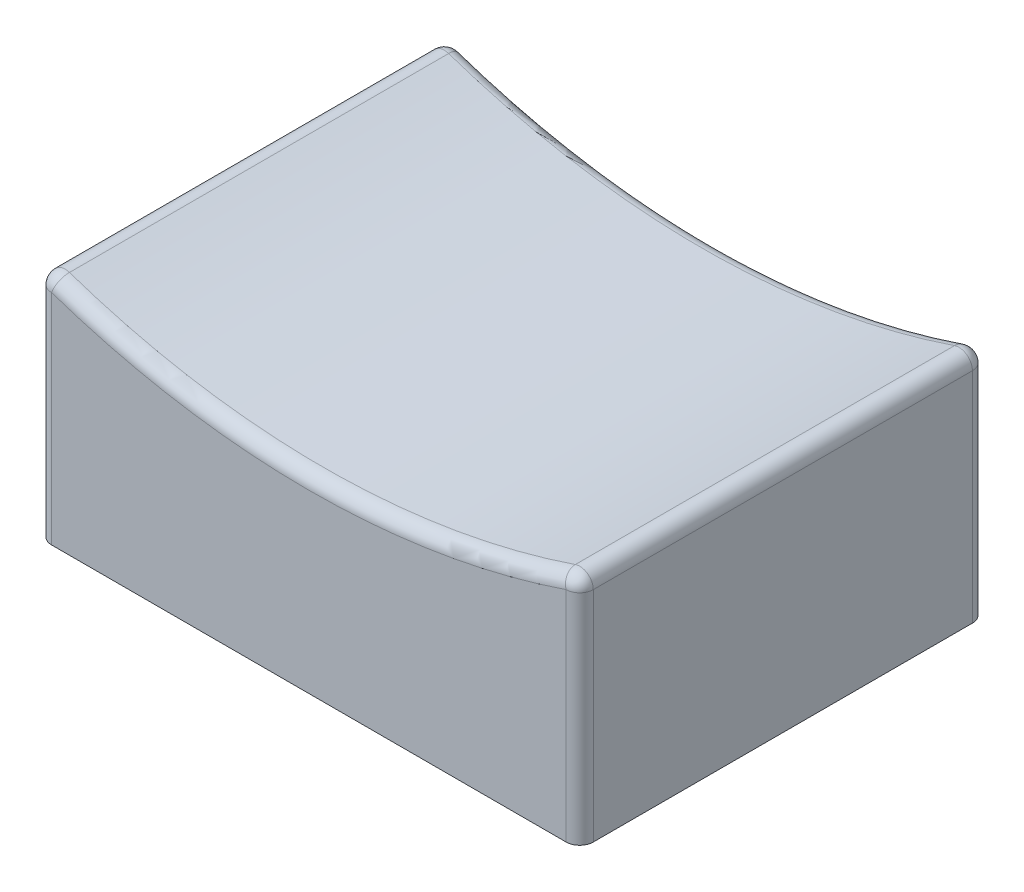
SolidWorks part; units mm, degrees
material "PBT General Purpose"
ref_plane "Front Plane" through (0, 0, 0) normal (0, 0, 1) x (1, 0, 0)
ref_plane "Top Plane" through (0, 0, 0) normal (0, 1, 0) x (1, 0, 0)
ref_plane "Right Plane" through (0, 0, 0) normal (1, 0, 0) x (0, 0, -1)
sketch "Sketch1" plane through (0, 0, 0) normal (0, 0, 1) x (1, 0, 0)
  line L0 (10, 0) -> (10, 36) construction
  line L1 (0, 0) -> (20, 0)
  line L2 (0, 0) -> (0, 8.7787)
  line L4 (20, 0) -> (20, 8.7787)
  arc A0 (0, 8.7787) -> (20, 8.7787) centre (10, 36) ccw
  point P8 (10, 7)
  dimension "D1" = 58
  dimension "D2" = 7
  dimension "D3" = 20
extrude "Boss-Extrude1" add sketch "Sketch1" along normal blind 15
fillet "Fillet1" radius 0.5 8 edges at (20, 8.7787, 7.5) (10, 7, 15) (0, 8.7787, 7.5) (10, 7, 0) (20, 4.3893, 0) (0, 4.3893, 0) (20, 4.3893, 15) (0, 4.3893, 15)
